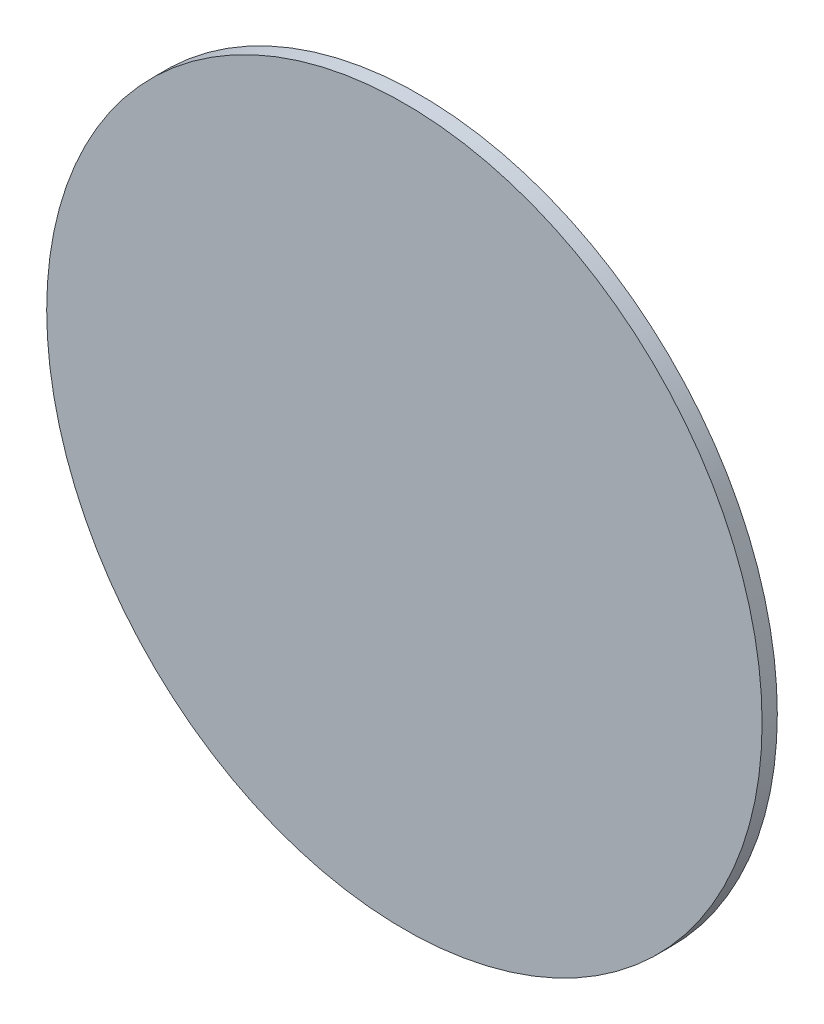
SolidWorks part; units mm, degrees
ref_plane "Front Plane" through (0, 0, 0) normal (0, 0, 1) x (1, 0, 0)
ref_plane "Top Plane" through (0, 0, 0) normal (0, 1, 0) x (1, 0, 0)
ref_plane "Right Plane" through (0, 0, 0) normal (1, 0, 0) x (0, 0, -1)
sketch "Sketch1" plane through (0, 0, 0) normal (0, 0, 1) x (1, 0, 0)
  circle A0 centre (0, 0) radius 5.969
  dimension "D1" = 11.938
extrude "Boss-Extrude1" add sketch "Sketch1" along normal blind 0.254
